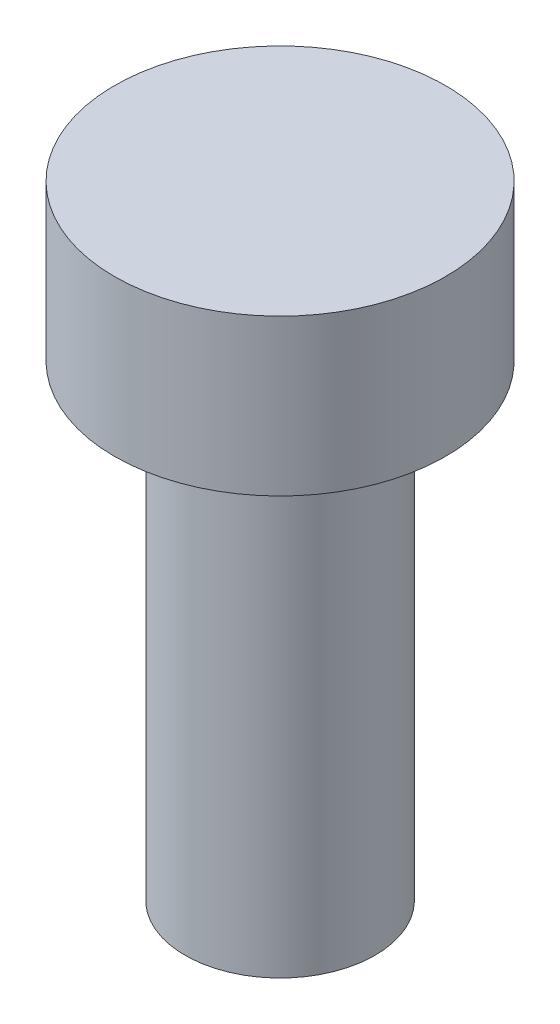
SolidWorks part; units mm, degrees
ref_plane "Front Plane" through (0, 0, 0) normal (0, 0, 1) x (1, 0, 0)
ref_plane "Top Plane" through (0, 0, 0) normal (0, 1, 0) x (1, 0, 0)
ref_plane "Right Plane" through (0, 0, 0) normal (1, 0, 0) x (0, 0, -1)
sketch "Sketch1" plane through (0, 0, 0) normal (0, 1, 0) x (1, 0, 0)
  circle A0 centre (0, 0) radius 4.25
  dimension "D1" = 8.5
extrude "Boss-Extrude1" add sketch "Sketch1" along normal blind 4
sketch "Sketch2" plane through (0, 0, 0) normal (0, -1, 0) x (1, 0, 0)
  circle A0 centre (0, 0) radius 2.44
  dimension "D1" = 4.88
extrude "Boss-Extrude2" add sketch "Sketch2" along normal blind 12
